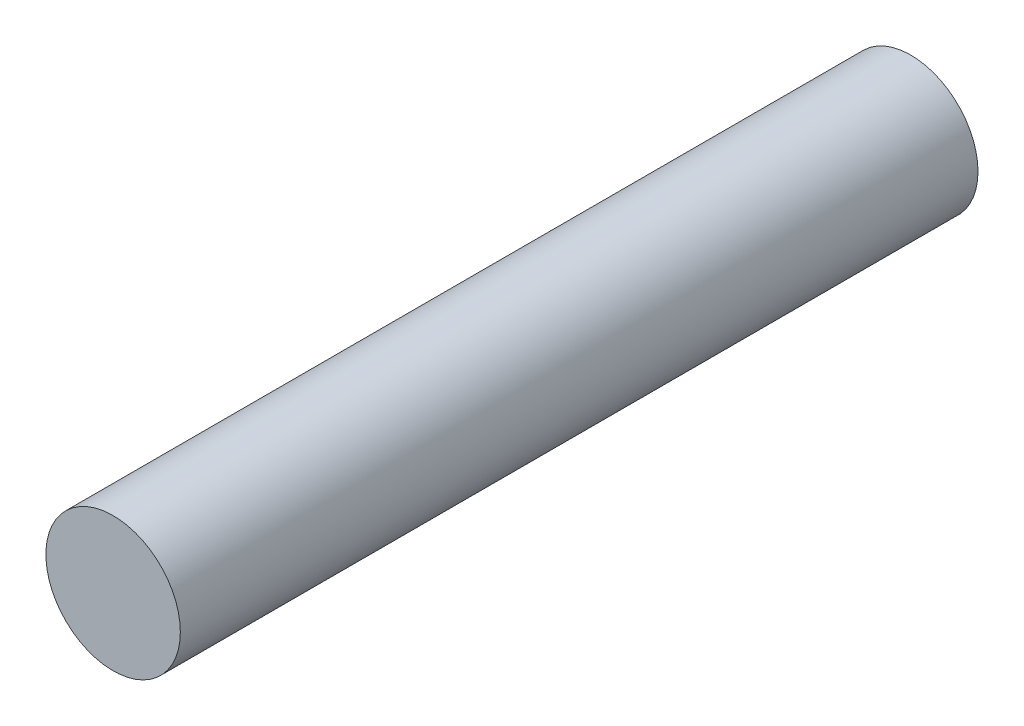
SolidWorks part; units mm, degrees
ref_plane "Front Plane" through (0, 0, 0) normal (0, 0, 1) x (1, 0, 0)
ref_plane "Top Plane" through (0, 0, 0) normal (0, 1, 0) x (1, 0, 0)
ref_plane "Right Plane" through (0, 0, 0) normal (1, 0, 0) x (0, 0, -1)
sketch "Sketch1" plane through (0, 0, 0) normal (0, 0, 1) x (1, 0, 0)
  circle A0 centre (0, 0) radius 2.95
  dimension "D1" = 5.9
extrude "Boss-Extrude1" add sketch "Sketch1" along normal blind 35
sketch "Sketch2" plane through (0, 0, 0) normal (0, 0, -1) x (-1, 0, 0)
  line L0 (-1.2961, 1.51) -> (1.2961, 1.51)
  arc A0 (-1.2961, 1.51) -> (1.2961, 1.51) centre (0, 0) ccw
  point P1 (0, -1.99)
  dimension "D1" = 3.5
  dimension "D2" = 1.99
extrude "Cut-Extrude1" cut sketch "Sketch2" against normal blind 7
